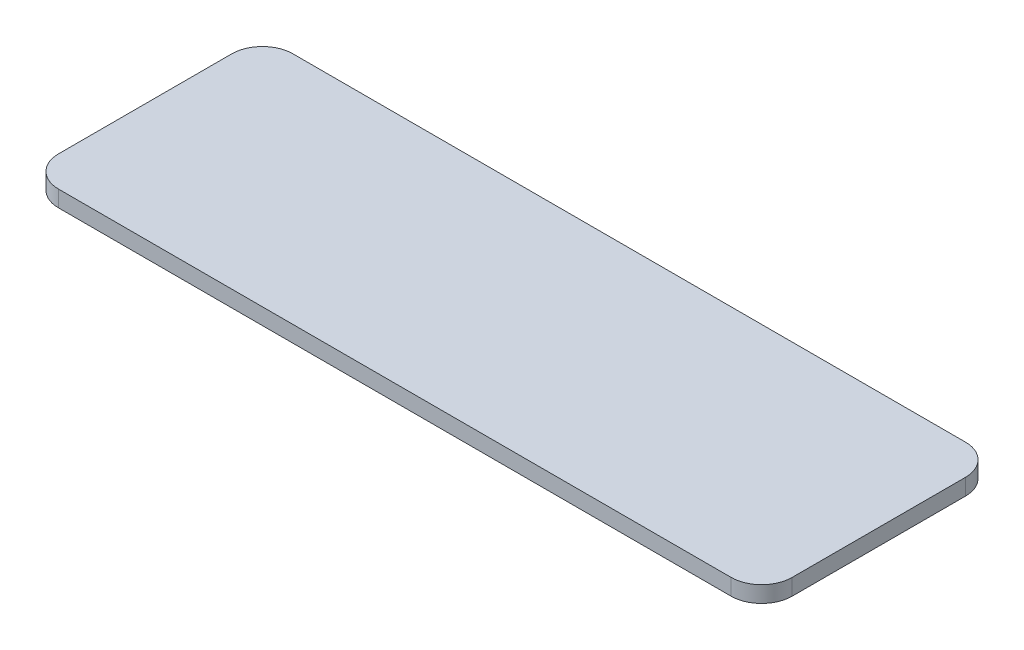
SolidWorks part; units mm, degrees
ref_plane "Front Plane" through (0, 0, 0) normal (0, 0, 1) x (1, 0, 0)
ref_plane "Top Plane" through (0, 0, 0) normal (0, 1, 0) x (1, 0, 0)
ref_plane "Right Plane" through (0, 0, 0) normal (1, 0, 0) x (0, 0, -1)
sketch "Sketch1" plane through (0, 0, 0) normal (0, 1, 0) x (1, 0, 0)
  line L1 (3, 0) -> (69, 0)
  line L2 (0, 3) -> (0, 20)
  line L3 (3, 23) -> (69, 23)
  line L4 (72, 3) -> (72, 20)
  arc A0 (3, 0) -> (0, 3) centre (3, 3) cw
  arc A1 (69, 0) -> (72, 3) centre (69, 3) ccw
  arc A2 (69, 23) -> (72, 20) centre (69, 20) cw
  arc A3 (0, 20) -> (3, 23) centre (3, 20) cw
  point P7 (0, 0)
  point P10 (72, 0)
  point P13 (72, 23)
  dimension "D3" = 3
  dimension "D1" = 72
  dimension "D2" = 23
extrude "Boss-Extrude1" add sketch "Sketch1" along normal blind 1.6
sketch "Sketch2" plane through (0, 1.6, 0) normal (0, 1, 0) x (1, 0, 0)
  line L0 (69, 23) -> (3, 23) construction
  line L1 (72, 3) -> (72, 20) construction
  point P0 (64, 16)
  point P1 (46, 16)
  point P2 (28, 16)
  dimension "D1" = 7
  dimension "D2" = 8
  dimension "D3" = 26
  dimension "D4" = 44
sketch "Sketch3" plane through (0, 1.6, 0) normal (0, 1, 0) x (1, 0, 0)
  line L0 (69, 23) -> (3, 23) construction
  line L1 (72, 3) -> (72, 20) construction
  point P0 (10, 16)
  dimension "D1" = 7
  dimension "D2" = 62
